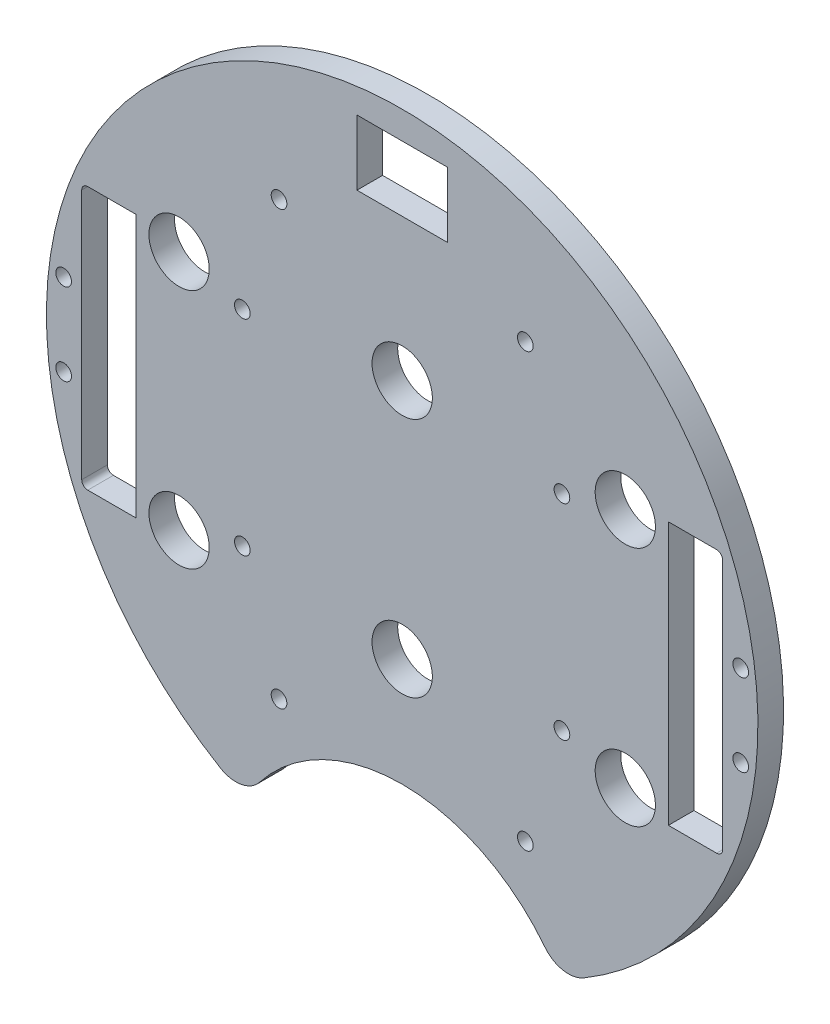
SolidWorks part; units mm, degrees
ref_plane "Front Plane" through (0, 0, 0) normal (0, 0, 1) x (1, 0, 0)
ref_plane "Top Plane" through (0, 0, 0) normal (0, 1, 0) x (1, 0, 0)
ref_plane "Right Plane" through (0, 0, 0) normal (1, 0, 0) x (0, 0, -1)
sketch "Sketch1" plane through (0, 0, 0) normal (0, 0, 1) x (1, 0, 0)
  line L0 (0, 0) -> (-82.1241, 0) construction
  line L1 (0, 0) -> (0, 95.6219) construction
  line L2 (67.494, 26.416) -> (67.494, -26.416)
  line L3 (-66.224, 27.686) -> (-56.064, 27.686)
  line L4 (-67.494, 26.416) -> (-67.494, -26.416)
  line L5 (-66.224, -27.686) -> (-56.064, -27.686)
  line L6 (-56.064, 27.686) -> (-56.064, -27.686)
  line L7 (66.224, -27.686) -> (56.064, -27.686)
  line L8 (66.224, 27.686) -> (56.064, 27.686)
  line L9 (56.064, 27.686) -> (56.064, -27.686)
  arc A0 (-69.526, -27.94) -> (69.526, -27.94) centre (0, 0) ccw
  arc A9 (69.526, 27.94) -> (-69.526, 27.94) centre (0, 0) ccw
  circle A10 centre (0, 0) radius 74.93
  arc A11 (66.224, 27.686) -> (67.494, 26.416) centre (66.224, 26.416) cw
  arc A12 (66.224, -27.686) -> (67.494, -26.416) centre (66.224, -26.416) ccw
  arc A13 (-66.224, 27.686) -> (-67.494, 26.416) centre (-66.224, 26.416) ccw
  arc A14 (-66.224, -27.686) -> (-67.494, -26.416) centre (-66.224, -26.416) cw
  dimension "D13" = 1.27
  dimension "D14" = 1.27
  dimension "D6" = 1.27
  dimension "D7" = 55.372
  dimension "D11" = 27.686
  dimension "D15" = 11.43
extrude "Boss-Extrude2" add sketch "Sketch1" along normal blind 5.3975
sketch "Sketch2" plane through (0, 0, 5.3975) normal (0, 0, 1) x (1, 0, 0)
  line L1 (-9.525, 69.088) -> (9.525, 69.088)
  line L2 (-9.525, 69.088) -> (-9.525, 55.372)
  line L3 (-9.525, 55.372) -> (9.525, 55.372)
  line L4 (9.525, 69.088) -> (9.525, 55.372)
  circle A3 centre (0, 0) radius 74.93 construction
  dimension "D1" = 19.05
  dimension "D2" = 13.716
  dimension "D3" = 55.372
extrude "Cut-Extrude1" cut sketch "Sketch2" against normal through all
sketch "Sketch3" plane through (0, 0, 5.3975) normal (0, 0, 1) x (1, 0, 0)
  line L0 (0, 0) -> (0, -68.8477) construction
  line L1 (-33.02, -67.2621) -> (33.02, -67.2621)
  circle A0 centre (0, 0) radius 74.93 construction
  circle A3 centre (0, -86.3121) radius 38.1
  dimension "D1" = 66.04
  dimension "D2" = 76.2
  dimension "D3" = 0
  dimension "D4" = 19.05
extrude "Cut-Extrude2" cut sketch "Sketch3" against normal through all
extrude "Cut-Extrude3" cut sketch "Sketch4" against normal through all
sketch "Sketch4" plane through (-31.3134, 132.559, 19.05) normal (0, 0, 1) x (0, 1, 0)
  line L0 (-132.559, -31.3134) -> (-245.9178, -31.3134) construction
  line L1 (-132.559, -31.3134) -> (-132.559, -129.4011) construction
  circle A0 centre (-180.819, -4.6434) radius 1.651
  circle A3 centre (-180.819, -57.9834) radius 1.651
  circle A4 centre (-84.299, -57.9834) radius 1.651
  circle A5 centre (-84.299, -4.6434) radius 1.651
extrude "Cut-Extrude4" cut sketch "Sketch5" against normal through all both and the other way through all
sketch "Sketch5" plane through (-31.3134, 132.614, 50.8) normal (0, 0, 1) x (0, 1, 0)
  line L0 (-132.614, -31.3134) -> (-132.614, 57.8454) construction
  line L1 (-132.614, -31.3134) -> (-222.516, -31.3134) construction
  circle A0 centre (-158.014, 14.4066) radius 3.175
  circle A1 centre (-173.254, -31.3134) radius 3.175
  circle A3 centre (-158.014, -77.0334) radius 3.175
  circle A4 centre (-107.214, -77.0334) radius 3.175
  circle A5 centre (-91.974, -31.3134) radius 3.175
  circle A6 centre (-107.214, 14.4066) radius 3.175
fillet "Fillet1" radius 6.35 2 edges at (-33.001, -67.2714, 2.6987) (33.001, -67.2714, 2.6987)
extrude "Cut-Extrude7" cut sketch "Sketch8" against normal blind 75.692
sketch "Sketch8" plane through (30.092, 4.0835, -11.4935) normal (0, 0, -1) x (-1, 0, 0)
  circle A0 centre (63.7572, 17.5065) radius 1.651
  circle A1 centre (63.7572, -25.6735) radius 1.651
  circle A2 centre (-3.5528, -25.6735) radius 1.651
  circle A3 centre (-3.5528, 17.5065) radius 1.651
extrude "Cut-Extrude9" cut sketch "Sketch10" against normal blind 97.79
sketch "Sketch10" plane through (30.092, 4.0835, -41.529) normal (0, 0, -1) x (-1, 0, 0)
  line L0 (30.092, -29.4835) -> (30.092, 6.2385) construction
  circle A0 centre (4.1544, -49.7288) radius 1.651
  circle A4 centre (56.0296, -49.7288) radius 1.651
  circle A5 centre (4.1544, 41.3825) radius 1.651
  circle A9 centre (56.0296, 41.3825) radius 1.651
extrude "Cut-Extrude10" cut sketch "Sketch11" against normal blind 150.876
sketch "Sketch11" plane through (30.092, 4.0835, 5.3975) normal (0, 0, 1) x (1, 0, 0)
  circle A0 centre (-101.396, -12.7195) radius 1.651
  circle A1 centre (-101.396, 4.5525) radius 1.651
  circle A2 centre (41.212, -12.7195) radius 1.651
  circle A3 centre (41.212, 4.5525) radius 1.651
extrude "Cut-Extrude11" cut sketch "Sketch12" against normal blind 48.768 and the other way blind 103.378
sketch "Sketch12" plane through (30.092, 4.0835, -5.3975) normal (0, 0, -1) x (-1, 0, 0)
  line L0 (30.092, -4.0835) -> (148.6336, -4.0835) construction
  line L1 (30.092, -4.0835) -> (30.092, 90.452) construction
  circle A0 centre (-16.898, 21.3165) radius 3.175
  circle A1 centre (77.082, 21.3165) radius 3.175
  circle A2 centre (30.092, 21.3165) radius 3.175
  circle A4 centre (77.082, -29.4835) radius 3.175
  circle A5 centre (30.092, -29.4835) radius 3.175
  circle A6 centre (-16.898, -29.4835) radius 3.175
sketch "Sketch13" plane through (0, 0, 0) normal (0, 0, -1) x (-1, 0, 0)
  circle A0 centre (46.99, 25.4) radius 6.35
  circle A1 centre (0, 25.4) radius 6.35
  circle A2 centre (-46.99, 25.4) radius 6.35
  circle A3 centre (-46.99, -25.4) radius 6.35
  circle A4 centre (0, -25.4) radius 6.35
  circle A5 centre (46.99, -25.4) radius 6.35
  dimension "D1" = 12.7
  dimension "D2" = 12.7
  dimension "D3" = 12.7
  dimension "D4" = 12.7
  dimension "D5" = 12.7
  dimension "D6" = 12.7
extrude "Cut-Extrude12" cut sketch "Sketch13" against normal blind 26.416
